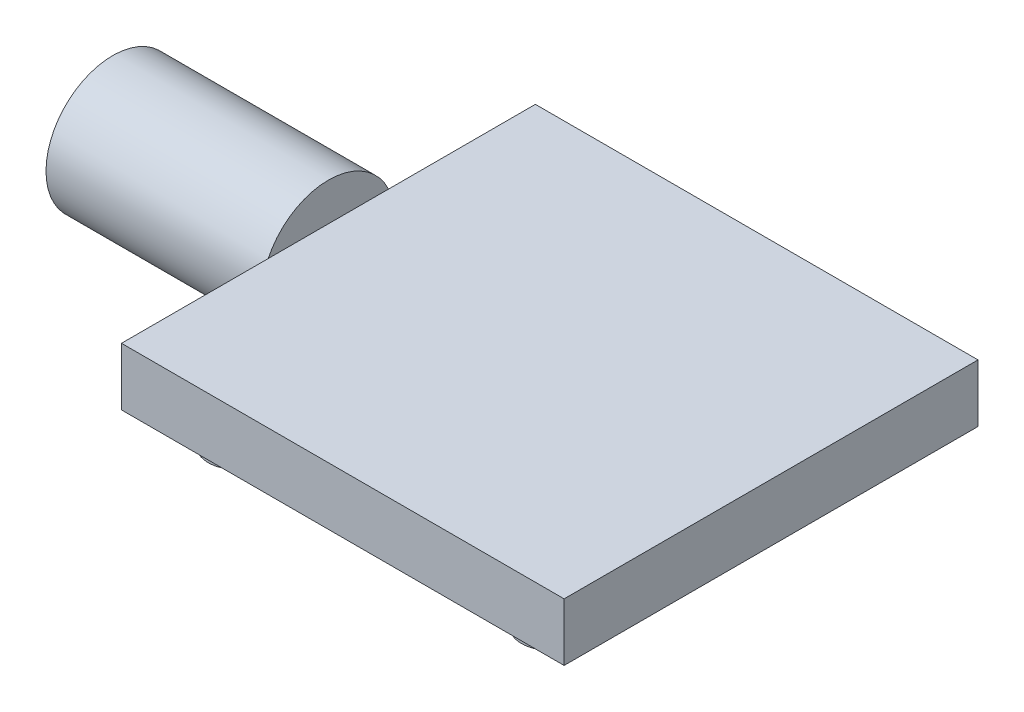
SolidWorks part; units mm, degrees
ref_plane "Front Plane" through (0, 0, 0) normal (0, 0, 1) x (1, 0, 0)
ref_plane "Top Plane" through (0, 0, 0) normal (0, 1, 0) x (1, 0, 0)
ref_plane "Right Plane" through (0, 0, 0) normal (1, 0, 0) x (0, 0, -1)
sketch "Sketch1" plane through (0, 0, 0) normal (0, 1, 0) x (1, 0, 0)
  line L1 (-21.55, -20.15) -> (21.55, -20.15)
  line L2 (-21.55, -20.15) -> (-21.55, 20.15)
  line L3 (-21.55, 20.15) -> (21.55, 20.15)
  line L4 (21.55, -20.15) -> (21.55, 20.15)
  line L5 (-21.55, -20.15) -> (21.55, 20.15) construction
  line L6 (-21.55, 20.15) -> (21.55, -20.15) construction
  point P0 (0, 0)
  dimension "D1" = 40.3
  dimension "D2" = 43.1
extrude "Boss-Extrude1" add sketch "Sketch1" along normal blind 5.62
sketch "Sketch2" plane through (0, 5.62, 0) normal (0, 1, 0) x (1, 0, 0)
  line L0 (0, 18.138) -> (0, -16.1381) construction
  line L1 (-20.0546, 0) -> (17.1103, 0) construction
  circle A0 centre (-15.25, 15.25) radius 1.75
  circle A2 centre (-15.25, 15.25) radius 2.75
  circle A3 centre (15.25, 15.25) radius 1.75
  circle A4 centre (15.25, 15.25) radius 2.75
  circle A5 centre (15.25, -15.25) radius 1.75
  circle A6 centre (15.25, -15.25) radius 2.75
  circle A7 centre (-15.25, -15.25) radius 1.75
  circle A8 centre (-15.25, -15.25) radius 2.75
  dimension "D1" = 3.5
  dimension "D2" = 5.5
  dimension "D3" = 15.25
  dimension "D4" = 15.25
extrude "Boss-Extrude2" add sketch "Sketch2" against normal blind 8
sketch "Sketch3" plane through (-21.55, 0, 0) normal (-1, 0, 0) x (0, 0, 1)
  circle A0 centre (0, 2.81) radius 6.5
  dimension "D1" = 13
extrude "Boss-Extrude3" add sketch "Sketch3" along normal blind 21
